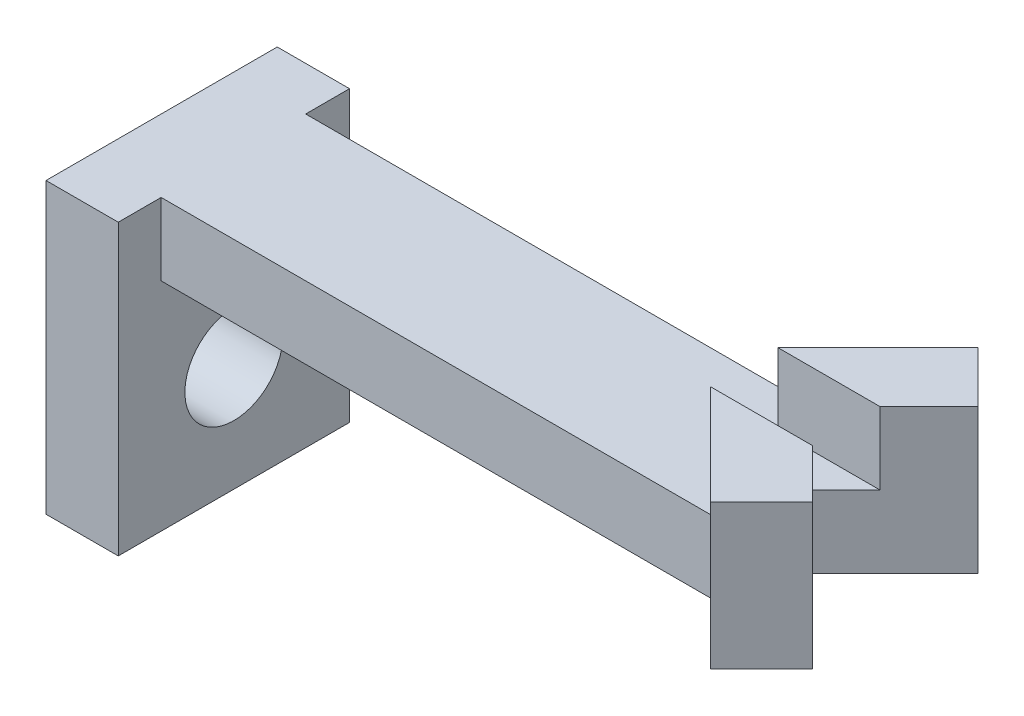
SolidWorks part; units mm, degrees
ref_plane "Front Plane" through (0, 0, 0) normal (0, 0, 1) x (1, 0, 0)
ref_plane "Top Plane" through (0, 0, 0) normal (0, 1, 0) x (1, 0, 0)
ref_plane "Right Plane" through (0, 0, 0) normal (1, 0, 0) x (0, 0, -1)
sketch "Sketch1" plane through (0, 0, 0) normal (0, 1, 0) x (1, 0, 0)
  line L0 (20.8258, -3.6548) -> (17.1915, -0.0205)
  line L1 (-11.4287, -3.1955) -> (15.8763, -3.1955)
  line L8 (15.8763, -3.1955) -> (18.5808, -5.8999)
  line L10 (18.5808, -5.8999) -> (20.8258, -3.6548)
  line L11 (-11.4287, -3.1955) -> (-11.4287, -0.0205)
  line L12 (15.8763, -3.1955) -> (12.7013, -0.0205) construction
  line L13 (-11.4287, -0.0205) -> (17.1915, -0.0205)
  point P0 (0, 0)
  point P1 (0, 0)
  point P3 (0, 0)
  point P6 (0, 0)
  point P9 (0, 0)
  point P11 (0, 0)
  point P13 (0, 0)
  point P14 (23.0709, -5.8999)
  point P15 (23.0709, -5.8999)
  point P16 (20.8303, -3.6593)
  point P17 (20.7553, -3.5843)
  dimension "D1" = 24.13
  dimension "D5" = 3.175
  dimension "D6" = 3.175
extrude "Boss-Extrude1" add sketch "Sketch1" along normal blind 3.175
mirror "Mirror1" about plane through (-11.4287, 3.175, 0.0205) normal (0, 0, 1) of "Boss-Extrude1"
sketch "Sketch2" plane through (0, 3.175, 0) normal (0, 1, 0) x (1, 0, 0)
  line L0 (18.5808, -5.8999) -> (14.1855, -1.5047)
  line L1 (14.1855, -1.5047) -> (18.6757, -1.5047)
  line L2 (20.8258, -3.6548) -> (17.1915, -0.0205) construction
  line L3 (18.6757, -1.5047) -> (20.8258, -3.6548)
  line L4 (20.8258, -3.6548) -> (18.5808, -5.8999)
  line L5 (17.1915, -0.0205) -> (11.2321, -0.0205) construction
  line L6 (18.6757, 1.4637) -> (20.8258, 3.6139)
  line L7 (14.1855, 1.4637) -> (18.6757, 1.4637)
  line L8 (18.5808, 5.859) -> (14.1855, 1.4637)
  line L10 (18.5808, 5.859) -> (20.8258, 3.6139)
extrude "Boss-Extrude2" add sketch "Sketch2" along normal blind 3.175
sketch "Sketch3" plane through (0, 3.175, 0) normal (0, 1, 0) x (1, 0, 0)
  line L0 (-11.4287, 3.1545) -> (-11.4287, -3.1955) construction
  line L1 (-11.4287, 5.08) -> (-8.2537, 5.08)
  line L2 (-11.4287, 5.08) -> (-11.4287, -5.08)
  line L3 (-11.4287, -5.08) -> (-8.2537, -5.08)
  line L4 (-8.2537, 5.08) -> (-8.2537, -5.08)
  line L5 (-11.4287, 5.08) -> (-8.2537, -5.08) construction
  line L6 (-11.4287, -5.08) -> (-8.2537, 5.08) construction
  point P0 (-9.8412, 0)
  point P5 (-9.3422, -0.276)
  point P8 (-9.8412, -0.0205)
  point P9 (-9.8412, 0)
  dimension "D1" = 3.175
  dimension "D2" = 10.16
extrude "Boss-Extrude3" add sketch "Sketch3" against normal blind 12.7
hole_wizard "#18 (0.1695) Diameter Hole1" positions "Sketch4" profile "Sketch5" hole size "#18" standard "ANSI Inch" end condition through all
sketch "Sketch4" plane through (-8.2537, 0, 0) normal (1, 0, 0) x (0, 0, -1)
  line L0 (-5.08, -9.525) -> (5.08, -9.525) construction
  point P0 (0, -4.7625)
  dimension "D1" = 4.7625
sketch "Sketch5" plane through (-8.2537, -4.7625, 0) normal (0, 1, 0) x (0, 0, -1)
  line L0 (0, 0) -> (0, 3.175)
  line L1 (0, 3.175) -> (2.1526, 3.175)
  line L2 (2.1526, 3.175) -> (2.1526, 0)
  line L5 (2.1526, 0) -> (0, 0)
  line L11 (0, -6.35) -> (0, 107.95) construction
  dimension "Thru Hole Dia." = 4.3053
  dimension "Thru Hole Depth" = 3.175
